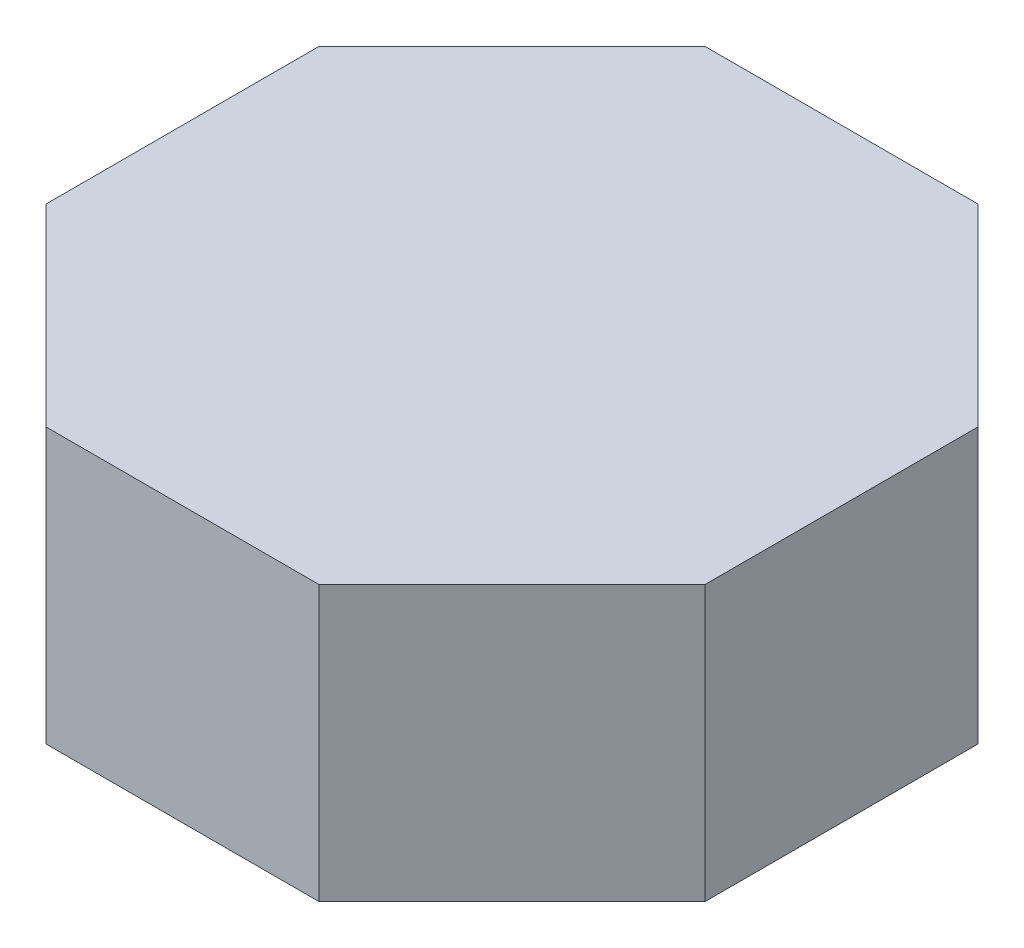
SolidWorks part; units mm, degrees
ref_plane "Alzado" through (0, 0, 0) normal (0, 0, 1) x (1, 0, 0)
ref_plane "Planta" through (0, 0, 0) normal (0, 1, 0) x (1, 0, 0)
ref_plane "Vista lateral" through (0, 0, 0) normal (1, 0, 0) x (0, 0, -1)
sketch "Croquis1" plane through (0, 0, 0) normal (0, 1, 0) x (1, 0, 0)
  line L1 (300, -124.2641) -> (300, 124.2641)
  line L2 (300, 124.2641) -> (124.2641, 300)
  line L3 (124.2641, 300) -> (-124.2641, 300)
  line L4 (-124.2641, 300) -> (-300, 124.2641)
  line L5 (-300, 124.2641) -> (-300, -124.2641)
  line L6 (-300, -124.2641) -> (-124.2641, -300)
  line L7 (-124.2641, -300) -> (124.2641, -300)
  line L8 (124.2641, -300) -> (300, -124.2641)
  circle A0 centre (0, 0) radius 300 construction
  dimension "D1" = 600
extrude "Saliente-Extruir1" add sketch "Croquis1" along normal blind 250
